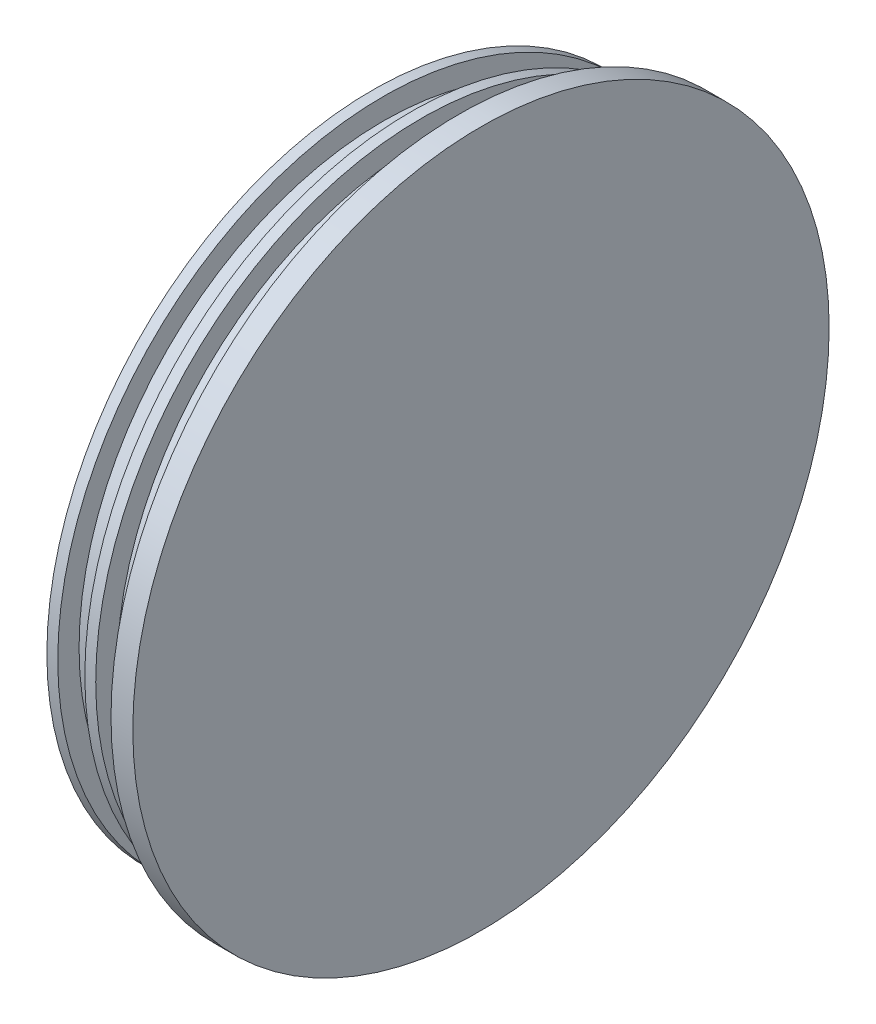
SolidWorks part; units mm, degrees
material "6061-T6 (SS)"
ref_plane "Front" through (0, 0, 0) normal (0, 0, 1) x (1, 0, 0)
ref_plane "Top" through (0, 0, 0) normal (0, 1, 0) x (1, 0, 0)
ref_plane "Right" through (0, 0, 0) normal (1, 0, 0) x (0, 0, -1)
sketch "Sketch1" plane through (0, 0, 0) normal (0, 0, 1) x (1, 0, 0)
  line L0 (4.318, 50.673) -> (4.318, 47.371)
  line L1 (-8.3185, 47.371) -> (-6.731, 47.371)
  line L2 (-8.3185, 47.371) -> (-8.3185, 41.0972)
  line L3 (-8.3185, 41.0972) -> (0, 41.0972)
  line L4 (0, 41.0972) -> (0, 0)
  line L5 (0, 0) -> (7.493, 0)
  line L6 (7.493, 0) -> (7.493, 50.673)
  line L7 (7.493, 50.673) -> (4.318, 50.673)
  line L8 (-6.731, 47.371) -> (-6.731, 44.2722)
  line L9 (-6.731, 44.2722) -> (-2.794, 44.2722)
  line L10 (-2.794, 44.2722) -> (-2.794, 47.371)
  line L11 (-2.794, 47.371) -> (-1.2065, 47.371)
  line L12 (-1.2065, 47.371) -> (-1.2065, 44.2722)
  line L13 (-1.2065, 44.2722) -> (2.7305, 44.2722)
  line L14 (2.7305, 44.2722) -> (2.7305, 47.371)
  line L15 (2.7305, 47.371) -> (4.318, 47.371)
  dimension "D1" = 3.175
  dimension "D2" = 50.673
  dimension "D3" = 3.302
  dimension "D4" = 3.937
  dimension "D5" = 3.0988
  dimension "D6" = 3.175
  dimension "D7" = 1.5875
  dimension "D8" = 7.493
revolve "Revolve1" add sketch "Sketch1" angle 360 about L5
hole_wizard "#6-32 Tapped Hole1" positions "Sketch3" profile "Sketch2" tap size "#6-32" standard "ANSI Inch"
sketch "Sketch3" plane through (0, 0, 0) normal (-1, 0, 0) x (0, 0, 1)
  line L0 (0, 9.779) -> (0, -9.779) construction
  line L2 (-9.779, 0) -> (9.779, 0) construction
  point P1 (0, 9.779)
  point P2 (0, -9.779)
  point P6 (-9.779, 0)
  point P7 (9.779, 0)
  dimension "D1" = 9.779
sketch "Sketch2" plane through (0, 9.779, 0) normal (0, 1, 0) x (0, 0, 1)
  line L0 (0, 0) -> (0, 5.1307)
  line L1 (0, 5.1307) -> (1.3525, 4.318)
  line L2 (1.3525, 4.318) -> (1.3525, 0)
  line L5 (1.3525, 0) -> (0, 0)
  line L10 (0, 5.1307) -> (-1.3526, 4.318) construction
  line L11 (0, -6.35) -> (0, 107.95) construction
  dimension "Tap Drill Dia." = 2.7051
  dimension "Tap Drill Depth" = 4.318
  dimension "Drill Angle" = 118
